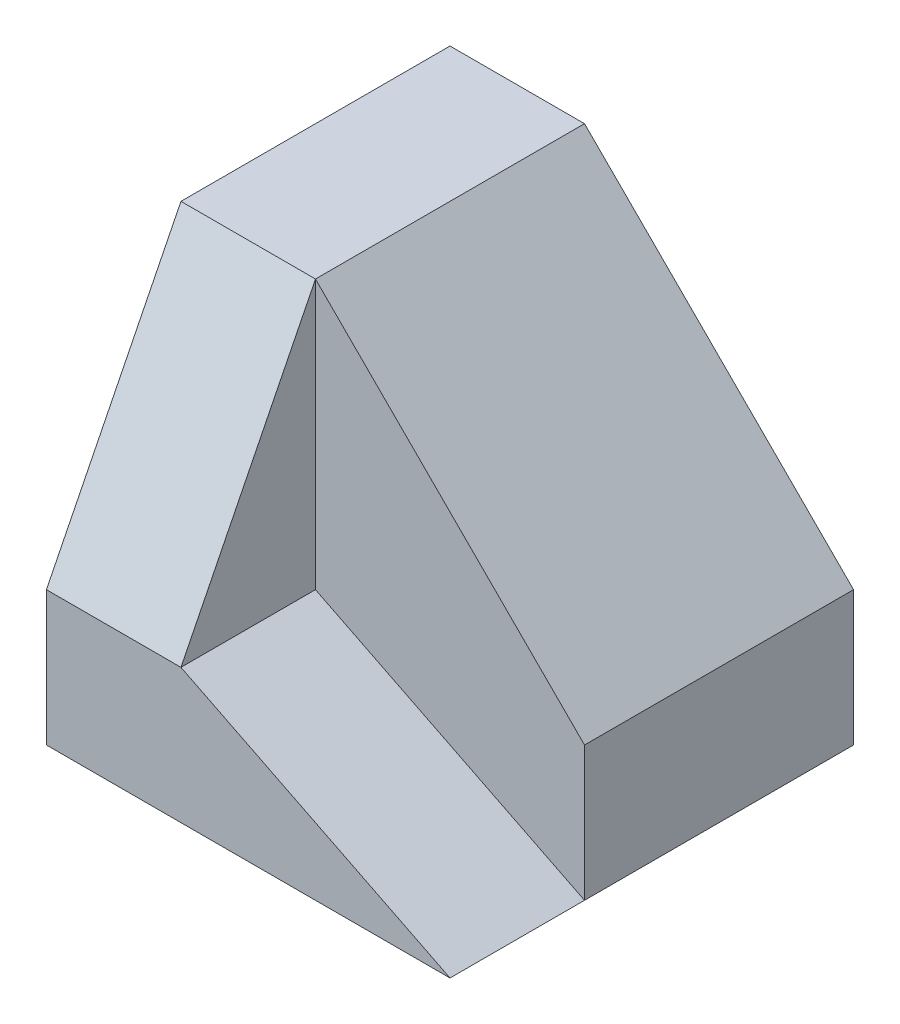
SolidWorks part; units mm, degrees
ref_plane "Alzado" through (0, 0, 0) normal (0, 0, 1) x (1, 0, 0)
ref_plane "Planta" through (0, 0, 0) normal (0, 1, 0) x (1, 0, 0)
ref_plane "Vista lateral" through (0, 0, 0) normal (1, 0, 0) x (0, 0, -1)
sketch "Croquis1" plane through (0, 0, 0) normal (0, 1, 0) x (1, 0, 0)
  line L1 (0, 0) -> (60, 0)
  line L2 (0, 0) -> (0, -60)
  line L3 (0, -60) -> (60, -60)
  line L4 (60, 0) -> (60, -60)
  dimension "D1" = 60
  dimension "D2" = 60
extrude "Saliente-Extruir1" add sketch "Croquis1" along normal blind 60
sketch "Croquis2" plane through (0, 0, 60) normal (0, 0, 1) x (1, 0, 0)
  line L0 (60, 60) -> (20, 60)
  line L1 (0, 60) -> (60, 60) construction
  line L2 (20, 60) -> (60, 20)
  line L3 (60, 60) -> (60, 0) construction
  line L4 (60, 20) -> (60, 60)
  dimension "D1" = 20
  dimension "D2" = 20
sketch "Croquis6" plane through (0, 60, 0) normal (0, 1, 0) x (1, 0, 0)
  line L1 (60, -60) -> (20, -60)
  line L2 (60, -60) -> (60, -40)
  line L3 (60, -40) -> (20, -40)
  line L4 (20, -60) -> (20, -40)
  dimension "D1" = 40
  dimension "D2" = 20
extrude "Cortar-Extruir2" cut sketch "Croquis6" against normal blind 40
extrude "Cortar-Extruir3" cut sketch "Croquis2" against normal blind 60
sketch "Croquis7" plane through (0, 0, 60) normal (0, 0, 1) x (1, 0, 0)
  line L0 (20, 20) -> (60, 0)
  line L1 (60, 0) -> (60, 20)
  line L2 (60, 20) -> (20, 20)
extrude "Cortar-Extruir4" cut sketch "Croquis7" against normal blind 20
sketch "Croquis8" plane through (20, 0, 0) normal (1, 0, 0) x (0, 0, -1)
  line L0 (-40, 60) -> (-60, 20)
  line L1 (-60, 20) -> (-60, 60)
  line L2 (-60, 60) -> (-40, 60)
extrude "Cortar-Extruir5" cut sketch "Croquis8" against normal blind 20
